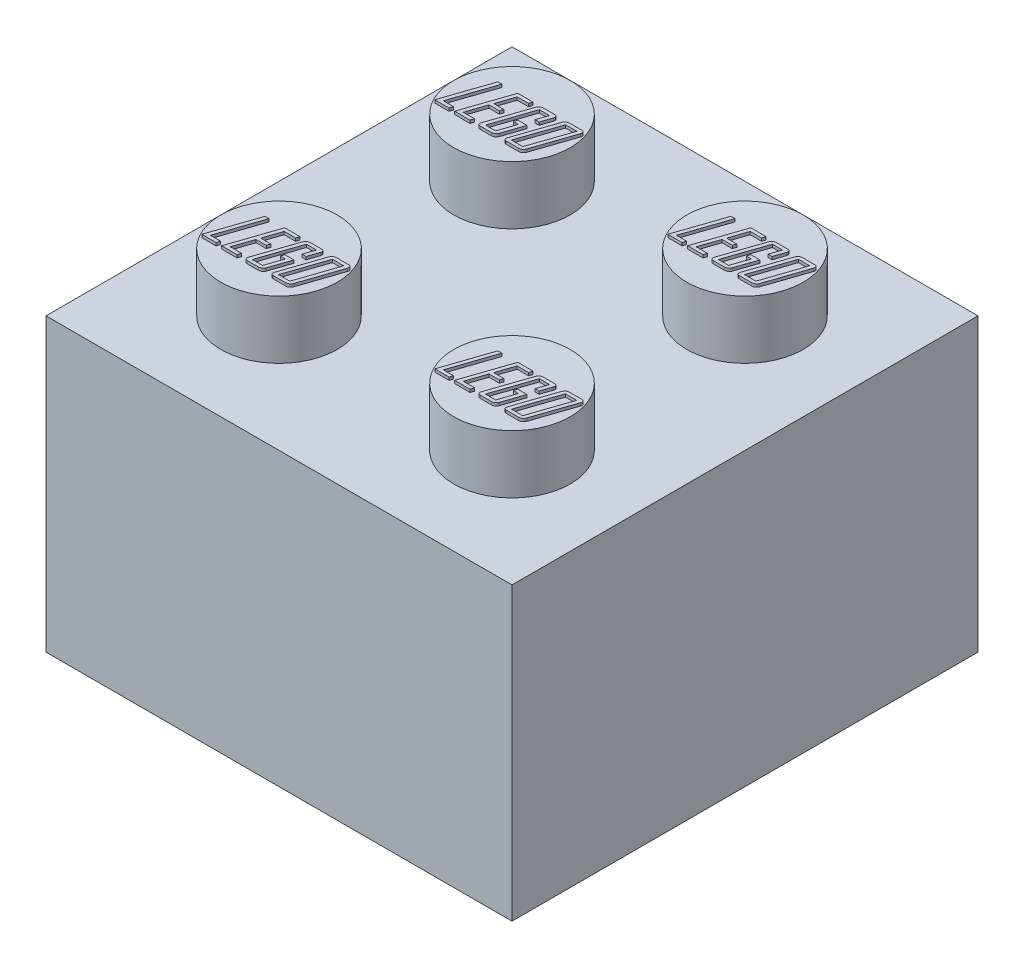
SolidWorks part; units mm, degrees
material "ABS"
ref_plane "Front Plane" through (0, 0, 0) normal (0, 0, 1) x (1, 0, 0)
ref_plane "Top Plane" through (0, 0, 0) normal (0, 1, 0) x (1, 0, 0)
ref_plane "Right Plane" through (0, 0, 0) normal (1, 0, 0) x (0, 0, -1)
sketch "Sketch1" plane through (0, 0, 0) normal (0, 1, 0) x (1, 0, 0)
  line L1 (8, -8) -> (-8, -8)
  line L2 (8, -8) -> (8, 8)
  line L3 (8, 8) -> (-8, 8)
  line L4 (-8, -8) -> (-8, 8)
  line L5 (8, -8) -> (-8, 8) construction
  line L6 (8, 8) -> (-8, -8) construction
  point P0 (0, 0)
  dimension "D1" = 16
  dimension "D2" = 16
extrude "Boss-Extrude1" add sketch "Sketch1" along normal blind 10
sketch "Sketch2" plane through (0, 10, 0) normal (0, 1, 0) x (1, 0, 0)
  line L0 (8, 0) -> (0, 0) construction
  line L1 (8, -8) -> (8, 8) construction
  line L2 (0, 0) -> (0, 8) construction
  line L3 (8, 8) -> (-8, 8) construction
  line L4 (-8, 8) -> (-8, -8) construction
  circle A0 centre (-4, 4) radius 2
  circle A1 centre (4, 4) radius 2
  circle A2 centre (4, -4) radius 2
  circle A3 centre (-4, -4) radius 2
  dimension "D1" = 4
  dimension "D2" = 4
  dimension "D3" = 4
extrude "Boss-Extrude2" add sketch "Sketch2" along normal blind 2
shell "Shell1" thickness 1
sketch "Sketch3" plane through (0, 9, 0) normal (0, -1, 0) x (1, 0, 0)
  circle A0 centre (0, 0) radius 2.7
  circle A1 centre (0, 0) radius 1.7
  dimension "D1" = 5.4
  dimension "D2" = 3.4
extrude "Boss-Extrude3" add sketch "Sketch3" along normal blind 9
sketch "Sketch4" plane through (0, 12, 0) normal (0, 1, 0) x (1, 0, 0)
  line L0 (6, -4) -> (2, -4) construction
  line L1 (2, -4) -> (2, -5) construction
  line L2 (2, -5) -> (5.7, -5) construction
  circle A0 centre (4, -4) radius 2 construction
  circle A1 centre (4, -4) radius 2 construction
  text T0 "<i>LEGO</i>" font "Agency FB" height in points 6
  dimension "D1" = 1
  dimension "D2" = 3.7
extrude "Boss-Extrude4" add sketch "Sketch4" along normal blind 0.1
sketch "Sketch6" plane through (0, 12, 0) normal (0, 1, 0) x (1, 0, 0)
  line L0 (-2, -4) -> (-6, -4) construction
  line L1 (-6, -4) -> (-6, -5) construction
  line L2 (-6, -5) -> (-2.3, -5) construction
  circle A0 centre (-4, -4) radius 2 construction
  circle A1 centre (-4, -4) radius 2 construction
  text T0 "<i>LEGO</i>" font "Agency FB" height in points 6
  dimension "D1" = 1
  dimension "D2" = 3.7
extrude "Boss-Extrude5" add sketch "Sketch6" along normal blind 0.1
sketch "Sketch7" plane through (0, 12, 0) normal (0, 1, 0) x (1, 0, 0)
  line L0 (-2, 4) -> (-6, 4) construction
  line L1 (-6, 4) -> (-6, 3) construction
  line L2 (-6, 3) -> (-2.3, 3) construction
  circle A0 centre (-4, 4) radius 2 construction
  circle A1 centre (-4, 4) radius 2 construction
  text T0 "<i>LEGO</i>" font "Agency FB" height in points 6
  dimension "D1" = 1
  dimension "D2" = 3.7
extrude "Boss-Extrude6" add sketch "Sketch7" along normal blind 0.1
sketch "Sketch8" plane through (0, 12, 0) normal (0, 1, 0) x (1, 0, 0)
  line L0 (6, 4) -> (2, 4) construction
  line L1 (2, 4) -> (2, 3) construction
  line L2 (2, 3) -> (5.7, 3) construction
  circle A0 centre (4, 4) radius 2 construction
  circle A1 centre (4, 4) radius 2 construction
  text T0 "<i>LEGO</i>" font "Agency FB" height in points 6
  dimension "D1" = 1
  dimension "D2" = 3.7
extrude "Boss-Extrude7" add sketch "Sketch8" along normal blind 0.1
